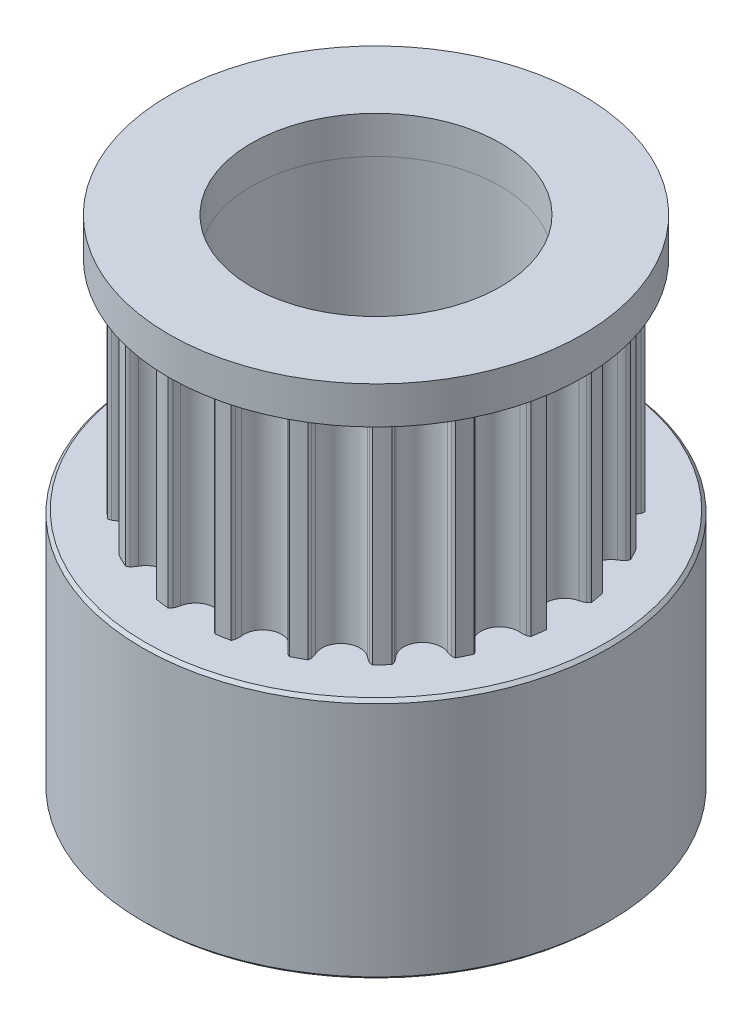
SolidWorks part; units mm, degrees
material "6061 slitina"
ref_plane "Přední rovina" through (0, 0, 0) normal (0, 0, 1) x (1, 0, 0)
ref_plane "Horní rovina" through (0, 0, 0) normal (0, 1, 0) x (1, 0, 0)
ref_plane "Pravá rovina" through (0, 0, 0) normal (1, 0, 0) x (0, 0, -1)
sketch "Skica1" plane through (0, 0, 0) normal (0, 1, 0) x (1, 0, 0)
  circle A0 centre (0, 0) radius 2.5
  arc B0 (-5.7301, 1.0983) -> (-5.3872, 2.2403) centre (-5.6803, 1.7058) ccw
  arc B1 (-5.7301, 1.0983) -> (-5.922, 1.0859) centre (-5.7841, 0.4401) ccw
  arc B2 (-5.922, 1.0859) -> (-6.0197, 1.0387) centre (-5.8743, 0.8624) ccw
  arc B3 (-6.0197, 1.0387) -> (-6.0791, 0.6004) centre (0, 0) ccw
  arc B4 (-6.0791, 0.6004) -> (-5.9974, 0.5289) centre (-5.892, 0.7317) ccw
  arc B5 (-5.9974, 0.5289) -> (-5.8158, 0.466) centre (-5.6927, 1.1148) ccw
  arc B6 (-5.7891, -0.7262) -> (-5.8158, 0.466) centre (-5.9294, -0.133) ccw
  arc B7 (-5.7891, -0.7262) -> (-5.9677, -0.7972) centre (-5.637, -1.3689) ccw
  arc B8 (-5.9677, -0.7972) -> (-6.0461, -0.8723) centre (-5.8532, -0.9951) ccw
  arc B9 (-6.0461, -0.8723) -> (-5.9671, -1.3075) centre (0, 0) ccw
  arc B10 (-5.9671, -1.3075) -> (-5.8673, -1.3503) centre (-5.8297, -1.1248) ccw
  arc B11 (-5.8673, -1.3503) -> (-5.6751, -1.354) centre (-5.7586, -0.6989) ccw
  arc B12 (-5.2813, -2.4796) -> (-5.6751, -1.354) centre (-5.5981, -1.9587) ccw
  arc B13 (-5.2813, -2.4796) -> (-5.4293, -2.6023) centre (-4.9381, -3.0438) ccw
  arc B14 (-5.4293, -2.6023) -> (-5.4806, -2.698) centre (-5.2593, -2.7551) ccw
  arc B15 (-5.4806, -2.698) -> (-5.271, -3.0875) centre (0, 0) ccw
  arc B16 (-5.271, -3.0875) -> (-5.1629, -3.0973) centre (-5.1968, -2.8713) ccw
  arc B17 (-5.1629, -3.0973) -> (-4.979, -3.0415) centre (-5.2608, -2.4442) ccw
  arc B18 (-4.2566, -3.9902) -> (-4.979, -3.0415) centre (-4.7188, -3.5928) ccw
  arc B19 (-4.2566, -3.9902) -> (-4.3594, -4.1527) centre (-3.7559, -4.4208) ccw
  arc B20 (-4.3594, -4.1527) -> (-4.3786, -4.2595) centre (-4.1505, -4.2455) ccw
  arc B21 (-4.3786, -4.2595) -> (-4.059, -4.5652) centre (0, 0) ccw
  arc B22 (-4.059, -4.5652) -> (-3.9531, -4.5412) centre (-4.0552, -4.3366) ccw
  arc B23 (-3.9531, -4.5412) -> (-3.7954, -4.4312) centre (-4.248, -3.9503) ccw
  arc B24 (-2.8152, -5.1103) -> (-3.7954, -4.4312) centre (-3.3776, -4.8751) ccw
  arc B25 (-2.8152, -5.1103) -> (-2.8628, -5.2965) centre (-2.2059, -5.3651) ccw
  arc B26 (-2.8628, -5.2965) -> (-2.8481, -5.4041) centre (-2.6354, -5.3203) ccw
  arc B27 (-2.8481, -5.4041) -> (-2.4496, -5.596) centre (0, 0) ccw
  arc B28 (-2.4496, -5.596) -> (-2.3563, -5.5405) centre (-2.5166, -5.3775) ccw
  arc B29 (-2.3563, -5.5405) -> (-2.2403, -5.3872) centre (-2.8194, -5.0696) ccw
  arc B30 (-1.0983, -5.7301) -> (-2.2403, -5.3872) centre (-1.7058, -5.6803) ccw
  arc B31 (-1.0983, -5.7301) -> (-1.0859, -5.922) centre (-0.4401, -5.7841) ccw
  arc B32 (-1.0859, -5.922) -> (-1.0387, -6.0197) centre (-0.8624, -5.8743) ccw
  arc B33 (-1.0387, -6.0197) -> (-0.6004, -6.0791) centre (0, 0) ccw
  arc B34 (-0.6004, -6.0791) -> (-0.5289, -5.9974) centre (-0.7317, -5.892) ccw
  arc B35 (-0.5289, -5.9974) -> (-0.466, -5.8158) centre (-1.1148, -5.6927) ccw
  arc B36 (0.7262, -5.7891) -> (-0.466, -5.8158) centre (0.133, -5.9294) ccw
  arc B37 (0.7262, -5.7891) -> (0.7972, -5.9677) centre (1.3689, -5.637) ccw
  arc B38 (0.7972, -5.9677) -> (0.8723, -6.0461) centre (0.9951, -5.8532) ccw
  arc B39 (0.8723, -6.0461) -> (1.3075, -5.9671) centre (0, 0) ccw
  arc B40 (1.3075, -5.9671) -> (1.3503, -5.8673) centre (1.1248, -5.8297) ccw
  arc B41 (1.3503, -5.8673) -> (1.354, -5.6751) centre (0.6989, -5.7586) ccw
  arc B42 (2.4796, -5.2813) -> (1.354, -5.6751) centre (1.9587, -5.5981) ccw
  arc B43 (2.4796, -5.2813) -> (2.6023, -5.4293) centre (3.0438, -4.9381) ccw
  arc B44 (2.6023, -5.4293) -> (2.698, -5.4806) centre (2.7551, -5.2593) ccw
  arc B45 (2.698, -5.4806) -> (3.0875, -5.271) centre (0, 0) ccw
  arc B46 (3.0875, -5.271) -> (3.0973, -5.1629) centre (2.8713, -5.1968) ccw
  arc B47 (3.0973, -5.1629) -> (3.0415, -4.979) centre (2.4442, -5.2608) ccw
  arc B48 (3.9902, -4.2566) -> (3.0415, -4.979) centre (3.5928, -4.7188) ccw
  arc B49 (3.9902, -4.2566) -> (4.1527, -4.3594) centre (4.4208, -3.7559) ccw
  arc B50 (4.1527, -4.3594) -> (4.2595, -4.3786) centre (4.2455, -4.1505) ccw
  arc B51 (4.2595, -4.3786) -> (4.5652, -4.059) centre (0, 0) ccw
  arc B52 (4.5652, -4.059) -> (4.5412, -3.9531) centre (4.3366, -4.0552) ccw
  arc B53 (4.5412, -3.9531) -> (4.4312, -3.7954) centre (3.9503, -4.248) ccw
  arc B54 (5.1103, -2.8152) -> (4.4312, -3.7954) centre (4.8751, -3.3776) ccw
  arc B55 (5.1103, -2.8152) -> (5.2965, -2.8628) centre (5.3651, -2.2059) ccw
  arc B56 (5.2965, -2.8628) -> (5.4041, -2.8481) centre (5.3203, -2.6354) ccw
  arc B57 (5.4041, -2.8481) -> (5.596, -2.4496) centre (0, 0) ccw
  arc B58 (5.596, -2.4496) -> (5.5405, -2.3563) centre (5.3775, -2.5166) ccw
  arc B59 (5.5405, -2.3563) -> (5.3872, -2.2403) centre (5.0696, -2.8194) ccw
  arc B60 (5.7301, -1.0983) -> (5.3872, -2.2403) centre (5.6803, -1.7058) ccw
  arc B61 (5.7301, -1.0983) -> (5.922, -1.0859) centre (5.7841, -0.4401) ccw
  arc B62 (5.922, -1.0859) -> (6.0197, -1.0387) centre (5.8743, -0.8624) ccw
  arc B63 (6.0197, -1.0387) -> (6.0791, -0.6004) centre (0, 0) ccw
  arc B64 (6.0791, -0.6004) -> (5.9974, -0.5289) centre (5.892, -0.7317) ccw
  arc B65 (5.9974, -0.5289) -> (5.8158, -0.466) centre (5.6927, -1.1148) ccw
  arc B66 (5.7891, 0.7262) -> (5.8158, -0.466) centre (5.9294, 0.133) ccw
  arc B67 (5.7891, 0.7262) -> (5.9677, 0.7972) centre (5.637, 1.3689) ccw
  arc B68 (5.9677, 0.7972) -> (6.0461, 0.8723) centre (5.8532, 0.9951) ccw
  arc B69 (6.0461, 0.8723) -> (5.9671, 1.3075) centre (0, 0) ccw
  arc B70 (5.9671, 1.3075) -> (5.8673, 1.3503) centre (5.8297, 1.1248) ccw
  arc B71 (5.8673, 1.3503) -> (5.6751, 1.354) centre (5.7586, 0.6989) ccw
  arc B72 (5.2813, 2.4796) -> (5.6751, 1.354) centre (5.5981, 1.9587) ccw
  arc B73 (5.2813, 2.4796) -> (5.4293, 2.6023) centre (4.9381, 3.0438) ccw
  arc B74 (5.4293, 2.6023) -> (5.4806, 2.698) centre (5.2593, 2.7551) ccw
  arc B75 (5.4806, 2.698) -> (5.271, 3.0875) centre (0, 0) ccw
  arc B76 (5.271, 3.0875) -> (5.1629, 3.0973) centre (5.1968, 2.8713) ccw
  arc B77 (5.1629, 3.0973) -> (4.979, 3.0415) centre (5.2608, 2.4442) ccw
  arc B78 (4.2566, 3.9902) -> (4.979, 3.0415) centre (4.7188, 3.5928) ccw
  arc B79 (4.2566, 3.9902) -> (4.3594, 4.1527) centre (3.7559, 4.4208) ccw
  arc B80 (4.3594, 4.1527) -> (4.3786, 4.2595) centre (4.1505, 4.2455) ccw
  arc B81 (4.3786, 4.2595) -> (4.059, 4.5652) centre (0, 0) ccw
  arc B82 (4.059, 4.5652) -> (3.9531, 4.5412) centre (4.0552, 4.3366) ccw
  arc B83 (3.9531, 4.5412) -> (3.7954, 4.4312) centre (4.248, 3.9503) ccw
  arc B84 (2.8152, 5.1103) -> (3.7954, 4.4312) centre (3.3776, 4.8751) ccw
  arc B85 (2.8152, 5.1103) -> (2.8628, 5.2965) centre (2.2059, 5.3651) ccw
  arc B86 (2.8628, 5.2965) -> (2.8481, 5.4041) centre (2.6354, 5.3203) ccw
  arc B87 (2.8481, 5.4041) -> (2.4496, 5.596) centre (0, 0) ccw
  arc B88 (2.4496, 5.596) -> (2.3563, 5.5405) centre (2.5166, 5.3775) ccw
  arc B89 (2.3563, 5.5405) -> (2.2403, 5.3872) centre (2.8194, 5.0696) ccw
  arc B90 (1.0983, 5.7301) -> (2.2403, 5.3872) centre (1.7058, 5.6803) ccw
  arc B91 (1.0983, 5.7301) -> (1.0859, 5.922) centre (0.4401, 5.7841) ccw
  arc B92 (1.0859, 5.922) -> (1.0387, 6.0197) centre (0.8624, 5.8743) ccw
  arc B93 (1.0387, 6.0197) -> (0.6004, 6.0791) centre (0, 0) ccw
  arc B94 (0.6004, 6.0791) -> (0.5289, 5.9974) centre (0.7317, 5.892) ccw
  arc B95 (0.5289, 5.9974) -> (0.466, 5.8158) centre (1.1148, 5.6927) ccw
  arc B96 (-0.7262, 5.7891) -> (0.466, 5.8158) centre (-0.133, 5.9294) ccw
  arc B97 (-0.7262, 5.7891) -> (-0.7972, 5.9677) centre (-1.3689, 5.637) ccw
  arc B98 (-0.7972, 5.9677) -> (-0.8723, 6.0461) centre (-0.9951, 5.8532) ccw
  arc B99 (-0.8723, 6.0461) -> (-1.3075, 5.9671) centre (0, 0) ccw
  arc B100 (-1.3075, 5.9671) -> (-1.3503, 5.8673) centre (-1.1248, 5.8297) ccw
  arc B101 (-1.3503, 5.8673) -> (-1.354, 5.6751) centre (-0.6989, 5.7586) ccw
  arc B102 (-2.4796, 5.2813) -> (-1.354, 5.6751) centre (-1.9587, 5.5981) ccw
  arc B103 (-2.4796, 5.2813) -> (-2.6023, 5.4293) centre (-3.0438, 4.9381) ccw
  arc B104 (-2.6023, 5.4293) -> (-2.698, 5.4806) centre (-2.7551, 5.2593) ccw
  arc B105 (-2.698, 5.4806) -> (-3.0875, 5.271) centre (0, 0) ccw
  arc B106 (-3.0875, 5.271) -> (-3.0973, 5.1629) centre (-2.8713, 5.1968) ccw
  arc B107 (-3.0973, 5.1629) -> (-3.0415, 4.979) centre (-2.4442, 5.2608) ccw
  arc B108 (-3.9902, 4.2566) -> (-3.0415, 4.979) centre (-3.5928, 4.7188) ccw
  arc B109 (-3.9902, 4.2566) -> (-4.1527, 4.3594) centre (-4.4208, 3.7559) ccw
  arc B110 (-4.1527, 4.3594) -> (-4.2595, 4.3786) centre (-4.2455, 4.1505) ccw
  arc B111 (-4.2595, 4.3786) -> (-4.5652, 4.059) centre (0, 0) ccw
  arc B112 (-4.5652, 4.059) -> (-4.5412, 3.9531) centre (-4.3366, 4.0552) ccw
  arc B113 (-4.5412, 3.9531) -> (-4.4312, 3.7954) centre (-3.9503, 4.248) ccw
  arc B114 (-5.1103, 2.8152) -> (-4.4312, 3.7954) centre (-4.8751, 3.3776) ccw
  arc B115 (-5.1103, 2.8152) -> (-5.2965, 2.8628) centre (-5.3651, 2.2059) ccw
  arc B116 (-5.2965, 2.8628) -> (-5.4041, 2.8481) centre (-5.3203, 2.6354) ccw
  arc B117 (-5.4041, 2.8481) -> (-5.596, 2.4496) centre (0, 0) ccw
  arc B118 (-5.596, 2.4496) -> (-5.5405, 2.3563) centre (-5.3775, 2.5166) ccw
  arc B119 (-5.5405, 2.3563) -> (-5.3872, 2.2403) centre (-5.0696, 2.8194) ccw
  dimension "D1" = 5
sketch_block_instance "Blok1-1"
sketch_block "Blok1"
extrude "Přidat vysunutím1" add sketch "Skica1" along normal blind 7 from offset 7.8
sketch "Skica2" plane through (0, 7.8, 0) normal (0, -1, 0) x (1, 0, 0)
  circle A0 centre (0, 0) radius 3.5
  circle A1 centre (0, 0) radius 2.5 construction
  circle A2 centre (0, 0) radius 2.5
  dimension "D1" = 7
extrude "Přidat vysunutím2" add sketch "Skica2" along normal blind 7.8
sketch "Skica3" plane through (0, 14.8, 0) normal (0, 1, 0) x (1, 0, 0)
  circle A0 centre (0, 0) radius 3.5
  circle A1 centre (0, 0) radius 2.5 construction
  circle A2 centre (0, 0) radius 2.5
  dimension "D1" = 7
extrude "Přidat vysunutím3" add sketch "Skica3" along normal blind 1.2
sketch "Skica5" plane through (0, 16, 0) normal (0, 1, 0) x (1, 0, 0)
  circle A0 centre (0, 0) radius 7.5
  circle A3 centre (0, 0) radius 3.5 construction
  circle A4 centre (0, 0) radius 3.5
  dimension "D1" = 15
extrude "Přidat vysunutím4" add sketch "Skica5" against normal up to surface (1.2 mm away) separate body up to face at (0, 14.8, 0)
sketch "Skica6" plane through (0, 0, 0) normal (0, -1, 0) x (1, 0, 0)
  circle A0 centre (0, 0) radius 7.5
  circle A1 centre (0, 0) radius 3.5 construction
  circle A2 centre (0, 0) radius 3.5
  circle A3 centre (0, 0) radius 7.5 construction
extrude "Přidat vysunutím5" add sketch "Skica6" against normal up to surface (7.8 mm away) separate body up to face at (0, 7.8, 0)
chamfer "Zkosení1" distance 0.1 angle 45 2 edges at (0, 14.8, 7.5) (0, 16, 7.5)
chamfer "Zkosení2" distance 0.1 angle 45 2 edges at (0, 0, -2.5) (0, 16, 2.5)
chamfer "Zkosení3" distance 0.1 angle 45 2 edges at (0, 0, -7.5) (0, 7.8, 7.5)
sketch "Sketch7" plane through (0, 0, 0) normal (0, -1, 0) x (1, 0, 0)
  circle A1 centre (0, 0) radius 4
extrude "Cut-Extrude1" cut sketch "Sketch7" against normal blind 20
sketch "Sketch8" plane through (0, 16, 0) normal (0, 1, 0) x (1, 0, 0)
  circle A0 centre (0, 0) radius 6.65
extrude "Cut-Extrude2" cut sketch "Sketch8" against normal blind 5 flip side to cut contours A0
ref_plane "Plane1" through (0, 0, -7.5) normal (0, 0, -1) x (-1, 0, 0)
ref_plane "Plane2" through (-7.5, 0, 0) normal (-1, 0, 0) x (0, 0, 1)
sketch "Sketch19" plane through (0, 0, -7.5) normal (0, 0, -1) x (-1, 0, 0)
  line L0 (0, 0.1) -> (0, 7.7)
  line L1 (7.5, 0.1) -> (-7.5, 0.1) construction
  line L2 (7.5, 7.7) -> (-7.5, 7.7) construction
  circle A0 centre (0, 3.9) radius 1.5
extrude "Cut-Extrude6" cut sketch "Sketch19" against normal blind 5 contours A0
sketch "Sketch20" plane through (-7.5, 0, 0) normal (-1, 0, 0) x (0, 0, 1)
  line L0 (0, 0.1) -> (0, 7.7)
  line L1 (-7.5, 0.1) -> (7.5, 0.1) construction
  line L2 (7.5, 7.7) -> (-7.5, 7.7) construction
  circle A0 centre (0, 3.9) radius 1.5
extrude "Cut-Extrude7" cut sketch "Sketch20" against normal blind 5 contours A0
